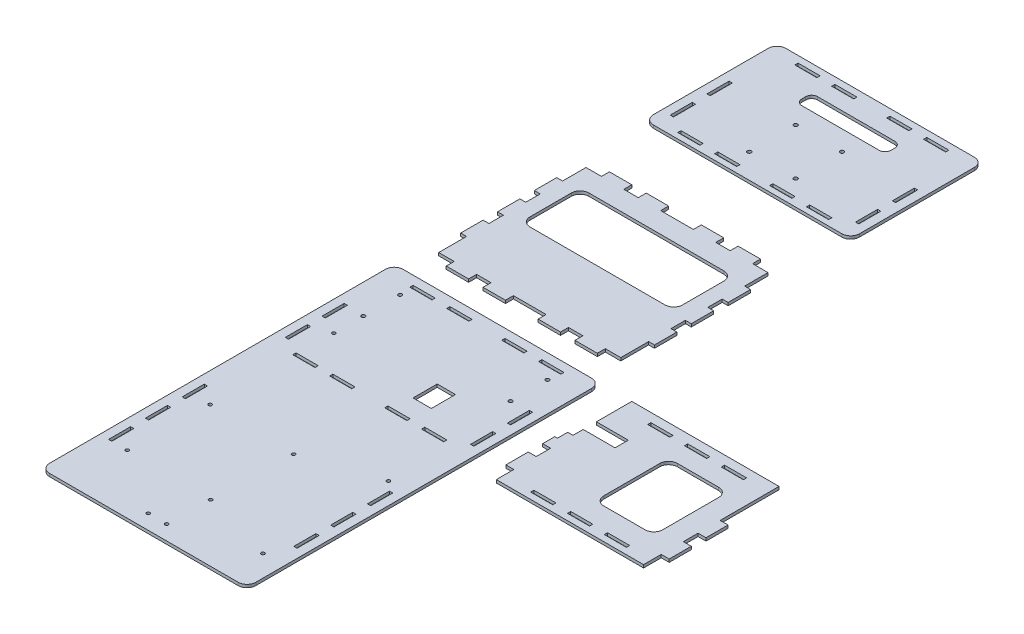
SolidWorks part; units mm, degrees
ref_plane "Front Plane" through (0, 0, 0) normal (0, 0, 1) x (1, 0, 0)
ref_plane "Top Plane" through (0, 0, 0) normal (0, 1, 0) x (1, 0, 0)
ref_plane "Right Plane" through (0, 0, 0) normal (1, 0, 0) x (0, 0, -1)
sketch "Sketch1" plane through (0, 0, 0) normal (0, 1, 0) x (1, 0, 0)
  line L0 (-154.6547, 109.6102) -> (-151.8607, 109.6102)
  line L1 (-154.6547, 192.1602) -> (7.9053, 192.1602)
  line L2 (-162.2747, 184.5402) -> (-162.2747, -105.0198)
  line L3 (-154.6547, -112.6398) -> (7.9053, -112.6398)
  line L4 (15.5253, 184.5402) -> (15.5253, -105.0198)
  line L5 (66.6776, 80.827) -> (66.6776, 83.621)
  line L6 (108.5876, 165.4902) -> (144.1476, 165.4902)
  line L7 (100.9676, 157.8702) -> (100.9676, 109.6102)
  line L8 (108.5876, 101.9902) -> (144.1476, 101.9902)
  line L9 (-154.6547, 109.6102) -> (-154.6547, 90.5602)
  line L10 (-154.6547, 90.5602) -> (-151.8607, 90.5602)
  line L11 (-151.8607, 109.6102) -> (-151.8607, 90.5602)
  line L12 (5.1113, 109.6102) -> (7.9053, 109.6102)
  line L13 (151.7676, 157.8702) -> (151.7676, 109.6102)
  line L14 (-154.6547, -11.0398) -> (-151.8607, -11.0398)
  line L15 (-154.6547, -11.0398) -> (-154.6547, -30.0898)
  line L16 (-154.6547, -30.0898) -> (-151.8607, -30.0898)
  line L17 (5.1113, 109.6102) -> (5.1113, 90.5602)
  line L18 (5.1113, 90.5602) -> (7.9053, 90.5602)
  line L19 (7.9053, 109.6102) -> (7.9053, 90.5602)
  line L20 (5.1113, 141.3602) -> (7.9053, 141.3602)
  line L21 (-154.6547, 141.3602) -> (-151.8607, 141.3602)
  line L22 (-154.6547, 141.3602) -> (-154.6547, 122.3102)
  line L23 (-154.6547, 122.3102) -> (-151.8607, 122.3102)
  line L24 (-151.8607, 141.3602) -> (-151.8607, 122.3102)
  line L25 (5.1113, 141.3602) -> (5.1113, 122.3102)
  line L26 (5.1113, 122.3102) -> (7.9053, 122.3102)
  line L27 (7.9053, 141.3602) -> (7.9053, 122.3102)
  line L28 (-106.6487, 80.827) -> (-106.6487, 83.621)
  line L29 (-106.6487, 80.827) -> (-87.5987, 80.827)
  line L30 (-87.5987, 80.827) -> (-87.5987, 83.621)
  line L31 (-106.6487, 83.621) -> (-87.5987, 83.621)
  line L32 (-138.3987, 80.827) -> (-138.3987, 83.621)
  line L33 (-138.3987, 80.827) -> (-119.3487, 80.827)
  line L34 (-119.3487, 80.827) -> (-119.3487, 83.621)
  line L35 (-138.3987, 83.621) -> (-119.3487, 83.621)
  line L36 (-27.4007, 80.827) -> (-27.4007, 83.621)
  line L37 (-27.4007, 80.827) -> (-8.3507, 80.827)
  line L38 (-8.3507, 80.827) -> (-8.3507, 83.621)
  line L39 (-27.4007, 83.621) -> (-8.3507, 83.621)
  line L40 (-59.1507, 80.827) -> (-59.1507, 83.621)
  line L41 (-59.1507, 80.827) -> (-40.1007, 80.827)
  line L42 (-40.1007, 80.827) -> (-40.1007, 83.621)
  line L43 (-59.1507, 83.621) -> (-40.1007, 83.621)
  line L44 (-106.6487, 181.7462) -> (-106.6487, 184.5402)
  line L45 (-106.6487, 181.7462) -> (-87.5987, 181.7462)
  line L46 (-87.5987, 181.7462) -> (-87.5987, 184.5402)
  line L47 (-106.6487, 184.5402) -> (-87.5987, 184.5402)
  line L48 (-138.3987, 181.7462) -> (-138.3987, 184.5402)
  line L49 (-138.3987, 181.7462) -> (-119.3487, 181.7462)
  line L50 (-119.3487, 181.7462) -> (-119.3487, 184.5402)
  line L51 (-138.3987, 184.5402) -> (-119.3487, 184.5402)
  line L52 (-27.4007, 181.7462) -> (-27.4007, 184.5402)
  line L53 (-27.4007, 181.7462) -> (-8.3507, 181.7462)
  line L54 (-8.3507, 181.7462) -> (-8.3507, 184.5402)
  line L55 (-27.4007, 184.5402) -> (-8.3507, 184.5402)
  line L56 (-59.1507, 181.7462) -> (-59.1507, 184.5402)
  line L57 (-59.1507, 181.7462) -> (-40.1007, 181.7462)
  line L58 (-40.1007, 181.7462) -> (-40.1007, 184.5402)
  line L59 (-59.1507, 184.5402) -> (-40.1007, 184.5402)
  line L60 (35.6896, 109.7372) -> (35.6896, 90.4332)
  line L61 (42.5476, 192.1602) -> (169.5476, 192.1602)
  line L62 (35.6896, 132.5972) -> (35.6896, 122.1832)
  line L63 (42.5476, 75.3202) -> (169.5476, 75.3202)
  line L64 (169.5476, 192.1602) -> (169.5476, 141.3602)
  line L65 (37.9756, 141.4872) -> (42.5476, 141.4872)
  line L66 (42.5476, 161.6802) -> (42.5476, 192.1602)
  line L67 (42.5476, 161.6802) -> (70.0304, 161.6802)
  line L68 (42.5476, 141.4872) -> (42.5476, 150.2502)
  line L69 (35.6896, 122.1832) -> (42.5476, 122.1832)
  line L70 (-106.7757, 213.2329) -> (-87.4717, 213.2329)
  line L71 (35.6896, 109.7372) -> (42.5476, 109.7372)
  line L72 (42.5476, 122.1832) -> (42.5476, 109.7372)
  line L73 (35.6896, 90.4332) -> (42.5476, 90.4332)
  line L74 (42.5476, 150.2502) -> (70.0304, 150.2502)
  line L75 (70.0304, 161.6802) -> (70.0304, 150.2502)
  line L76 (42.5476, 90.4332) -> (42.5476, 75.3202)
  line L77 (-59.2777, 213.2329) -> (-39.9737, 213.2329)
  line L78 (-119.2217, 213.2329) -> (-119.2217, 220.0909)
  line L79 (-119.2217, 220.0909) -> (-106.7757, 220.0909)
  line L80 (-106.7757, 213.2329) -> (-106.7757, 220.0909)
  line L81 (-27.5277, 213.2329) -> (-8.2237, 213.2329)
  line L82 (-87.4717, 213.2329) -> (-87.4717, 220.0909)
  line L83 (-87.4717, 220.0909) -> (-59.2777, 220.0909)
  line L84 (-59.2777, 213.2329) -> (-59.2777, 220.0909)
  line L85 (66.6776, 181.7462) -> (66.6776, 184.5402)
  line L86 (-39.9737, 213.2329) -> (-39.9737, 220.0909)
  line L87 (-39.9737, 220.0909) -> (-27.5277, 220.0909)
  line L88 (-27.5277, 213.2329) -> (-27.5277, 220.0909)
  line L89 (66.6776, 181.7462) -> (85.7276, 181.7462)
  line L90 (-8.2237, 213.2329) -> (-8.2237, 220.0909)
  line L91 (-8.2237, 220.0909) -> (5.1113, 220.0909)
  line L92 (85.7276, 181.7462) -> (85.7276, 184.5402)
  line L93 (-138.5257, 213.2329) -> (-119.2217, 213.2329)
  line L94 (-156.9407, 244.0939) -> (-156.9407, 263.3979)
  line L95 (-151.8607, 347.0909) -> (-138.5257, 347.0909)
  line L96 (10.1913, 244.0939) -> (10.1913, 263.3979)
  line L97 (66.6776, 184.5402) -> (85.7276, 184.5402)
  line L98 (-138.5257, 213.2329) -> (-138.5257, 220.0909)
  line L99 (-138.5257, 220.0909) -> (-151.8607, 220.0909)
  line L100 (130.1776, 181.7462) -> (130.1776, 184.5402)
  line L101 (130.1776, 181.7462) -> (149.2276, 181.7462)
  line L102 (149.2276, 181.7462) -> (149.2276, 184.5402)
  line L103 (130.1776, 184.5402) -> (149.2276, 184.5402)
  line L104 (98.4276, 181.7462) -> (98.4276, 184.5402)
  line L105 (98.4276, 181.7462) -> (117.4776, 181.7462)
  line L106 (117.4776, 181.7462) -> (117.4776, 184.5402)
  line L107 (98.4276, 184.5402) -> (117.4776, 184.5402)
  line L108 (-156.9407, 307.5939) -> (-156.9407, 326.8979)
  line L109 (-151.8607, -11.0398) -> (-151.8607, -30.0898)
  line L110 (5.1113, 347.0909) -> (5.1113, 326.8979)
  line L111 (5.1113, 326.8979) -> (10.1913, 326.8979)
  line L112 (-131.5407, 329.3109) -> (-15.2087, 329.3109)
  line L113 (10.1913, 307.5939) -> (5.1113, 307.5939)
  line L114 (10.1913, 307.5939) -> (10.1913, 326.8979)
  line L115 (10.1913, 295.1479) -> (5.1113, 295.1479)
  line L116 (5.1113, 307.5939) -> (5.1113, 295.1479)
  line L117 (10.1913, 275.8439) -> (5.1113, 275.8439)
  line L118 (-139.1607, 321.6909) -> (-139.1607, 286.1309)
  line L119 (10.1913, 263.3979) -> (5.1113, 263.3979)
  line L120 (5.1113, 275.8439) -> (5.1113, 263.3979)
  line L121 (10.1913, 244.0939) -> (5.1113, 244.0939)
  line L122 (10.1913, 275.8439) -> (10.1913, 295.1479)
  line L123 (-131.5407, 278.5109) -> (-15.2087, 278.5109)
  line L124 (5.1113, 244.0939) -> (5.1113, 220.0909)
  line L125 (-156.9407, 275.8439) -> (-156.9407, 295.1479)
  line L126 (-7.5887, 321.6909) -> (-7.5887, 286.1309)
  line L127 (-156.9407, 326.8979) -> (-151.8607, 326.8979)
  line L128 (-151.8607, 347.0909) -> (-151.8607, 326.8979)
  line L129 (-156.9407, 307.5939) -> (-151.8607, 307.5939)
  line L130 (-154.6547, -42.7898) -> (-151.8607, -42.7898)
  line L131 (-156.9407, 295.1479) -> (-151.8607, 295.1479)
  line L132 (-151.8607, 307.5939) -> (-151.8607, 295.1479)
  line L133 (-156.9407, 275.8439) -> (-151.8607, 275.8439)
  line L134 (-154.6547, -42.7898) -> (-154.6547, -61.8398)
  line L135 (-156.9407, 263.3979) -> (-151.8607, 263.3979)
  line L136 (-151.8607, 275.8439) -> (-151.8607, 263.3979)
  line L137 (-156.9407, 244.0939) -> (-151.8607, 244.0939)
  line L138 (-154.6547, -61.8398) -> (-151.8607, -61.8398)
  line L139 (-151.8607, -42.7898) -> (-151.8607, -61.8398)
  line L140 (-151.8607, 244.0939) -> (-151.8607, 220.0909)
  line L141 (5.1113, -11.0398) -> (7.9053, -11.0398)
  line L142 (5.1113, -11.0398) -> (5.1113, -30.0898)
  line L143 (5.1113, -30.0898) -> (7.9053, -30.0898)
  line L144 (7.9053, -11.0398) -> (7.9053, -30.0898)
  line L145 (7.9053, -42.7898) -> (5.1113, -42.7898)
  line L146 (7.9053, -42.7898) -> (7.9053, -61.8398)
  line L147 (7.9053, -61.8398) -> (5.1113, -61.8398)
  line L148 (5.1113, -42.7898) -> (5.1113, -61.8398)
  line L149 (5.1113, 1.6602) -> (7.9053, 1.6602)
  line L150 (5.1113, 1.6602) -> (5.1113, 20.7102)
  line L151 (5.1113, 20.7102) -> (7.9053, 20.7102)
  line L152 (7.9053, 1.6602) -> (7.9053, 20.7102)
  line L153 (-154.6547, 1.6602) -> (-151.8607, 1.6602)
  line L154 (-154.6547, 1.6602) -> (-154.6547, 20.7102)
  line L155 (-154.6547, 20.7102) -> (-151.8607, 20.7102)
  line L156 (-151.8607, 1.6602) -> (-151.8607, 20.7102)
  line L157 (-54.3315, 121.2429) -> (-38.5835, 121.2429)
  line L158 (-54.3315, 121.2429) -> (-54.3315, 100.4149)
  line L159 (-54.3315, 100.4149) -> (-38.5835, 100.4149)
  line L160 (-38.5835, 121.2429) -> (-38.5835, 100.4149)
  line L161 (66.6776, 80.827) -> (85.7276, 80.827)
  line L162 (85.7276, 80.827) -> (85.7276, 83.621)
  line L163 (66.6776, 83.621) -> (85.7276, 83.621)
  line L164 (130.1776, 80.827) -> (130.1776, 83.621)
  line L165 (130.1776, 80.827) -> (149.2276, 80.827)
  line L166 (149.2276, 80.827) -> (149.2276, 83.621)
  line L167 (130.1776, 83.621) -> (149.2276, 83.621)
  line L168 (98.4276, 80.827) -> (98.4276, 83.621)
  line L169 (98.4276, 80.827) -> (117.4776, 80.827)
  line L170 (117.4776, 80.827) -> (117.4776, 83.621)
  line L171 (98.4276, 83.621) -> (117.4776, 83.621)
  line L172 (169.5476, 122.3102) -> (169.5476, 109.6102)
  line L173 (169.5476, 90.5602) -> (176.4056, 90.5602)
  line L174 (-119.2217, 347.0909) -> (-106.7757, 347.0909)
  line L175 (35.6896, 132.5972) -> (37.9756, 132.5972)
  line L176 (37.9756, 141.4872) -> (37.9756, 132.5972)
  line L177 (169.5476, 109.6102) -> (176.4056, 109.6102)
  line L178 (176.4056, 90.5602) -> (176.4056, 109.6102)
  line L179 (169.5476, 122.3102) -> (176.4056, 122.3102)
  line L180 (169.5476, 90.5602) -> (169.5476, 75.3202)
  line L181 (169.5476, 141.3602) -> (176.4056, 141.3602)
  line L182 (176.4056, 122.3102) -> (176.4056, 141.3602)
  line L183 (-87.4717, 347.0909) -> (-59.2777, 347.0909)
  line L184 (-138.5257, 347.0909) -> (-138.5257, 353.9489)
  line L185 (-138.5257, 353.9489) -> (-119.2217, 353.9489)
  line L186 (-119.2217, 347.0909) -> (-119.2217, 353.9489)
  line L187 (-39.9737, 347.0909) -> (-27.5277, 347.0909)
  line L188 (-106.7757, 347.0909) -> (-106.7757, 353.9489)
  line L189 (-106.7757, 353.9489) -> (-87.4717, 353.9489)
  line L190 (-87.4717, 347.0909) -> (-87.4717, 353.9489)
  line L191 (-8.2237, 347.0909) -> (5.1113, 347.0909)
  line L192 (-59.2777, 347.0909) -> (-59.2777, 353.9489)
  line L193 (-59.2777, 353.9489) -> (-39.9737, 353.9489)
  line L194 (-39.9737, 347.0909) -> (-39.9737, 353.9489)
  line L195 (-154.6547, 441.5523) -> (-151.8607, 441.5523)
  line L196 (-27.5277, 347.0909) -> (-27.5277, 353.9489)
  line L197 (-27.5277, 353.9489) -> (-8.2237, 353.9489)
  line L198 (-8.2237, 347.0909) -> (-8.2237, 353.9489)
  line L199 (-154.6547, 407.9203) -> (7.9053, 407.9203)
  line L200 (-162.2747, 415.5403) -> (-162.2747, 514.6003)
  line L201 (-154.6547, 522.2203) -> (7.9053, 522.2203)
  line L202 (15.5253, 415.5403) -> (15.5253, 514.6003)
  line L203 (-154.6547, 441.5523) -> (-154.6547, 422.5023)
  line L204 (-154.6547, 422.5023) -> (-151.8607, 422.5023)
  line L205 (-151.8607, 441.5523) -> (-151.8607, 422.5023)
  line L206 (5.1113, 441.5523) -> (7.9053, 441.5523)
  line L207 (5.1113, 441.5523) -> (5.1113, 422.5023)
  line L208 (5.1113, 422.5023) -> (7.9053, 422.5023)
  line L209 (7.9053, 441.5523) -> (7.9053, 422.5023)
  line L210 (5.1113, 473.3023) -> (7.9053, 473.3023)
  line L211 (-154.6547, 473.3023) -> (-151.8607, 473.3023)
  line L212 (-154.6547, 473.3023) -> (-154.6547, 454.2523)
  line L213 (-154.6547, 454.2523) -> (-151.8607, 454.2523)
  line L214 (-151.8607, 473.3023) -> (-151.8607, 454.2523)
  line L215 (5.1113, 473.3023) -> (5.1113, 454.2523)
  line L216 (5.1113, 454.2523) -> (7.9053, 454.2523)
  line L217 (7.9053, 473.3023) -> (7.9053, 454.2523)
  line L218 (-106.6487, 412.769) -> (-106.6487, 415.563)
  line L219 (-106.6487, 412.769) -> (-87.5987, 412.769)
  line L220 (-87.5987, 412.769) -> (-87.5987, 415.563)
  line L221 (-106.6487, 415.563) -> (-87.5987, 415.563)
  line L222 (-138.3987, 412.769) -> (-138.3987, 415.563)
  line L223 (-138.3987, 412.769) -> (-119.3487, 412.769)
  line L224 (-119.3487, 412.769) -> (-119.3487, 415.563)
  line L225 (-138.3987, 415.563) -> (-119.3487, 415.563)
  line L226 (-27.4007, 412.769) -> (-27.4007, 415.563)
  line L227 (-27.4007, 412.769) -> (-8.3507, 412.769)
  line L228 (-8.3507, 412.769) -> (-8.3507, 415.563)
  line L229 (-27.4007, 415.563) -> (-8.3507, 415.563)
  line L230 (-59.1507, 412.769) -> (-59.1507, 415.563)
  line L231 (-59.1507, 412.769) -> (-40.1007, 412.769)
  line L232 (-40.1007, 412.769) -> (-40.1007, 415.563)
  line L233 (-59.1507, 415.563) -> (-40.1007, 415.563)
  line L234 (-106.6487, 513.6883) -> (-106.6487, 516.4823)
  line L235 (-106.6487, 513.6883) -> (-87.5987, 513.6883)
  line L236 (-87.5987, 513.6883) -> (-87.5987, 516.4823)
  line L237 (-106.6487, 516.4823) -> (-87.5987, 516.4823)
  line L238 (-138.3987, 513.6883) -> (-138.3987, 516.4823)
  line L239 (-138.3987, 513.6883) -> (-119.3487, 513.6883)
  line L240 (-119.3487, 513.6883) -> (-119.3487, 516.4823)
  line L241 (-138.3987, 516.4823) -> (-119.3487, 516.4823)
  line L242 (-27.4007, 513.6883) -> (-27.4007, 516.4823)
  line L243 (-27.4007, 513.6883) -> (-8.3507, 513.6883)
  line L244 (-8.3507, 513.6883) -> (-8.3507, 516.4823)
  line L245 (-27.4007, 516.4823) -> (-8.3507, 516.4823)
  line L246 (-59.1507, 513.6883) -> (-59.1507, 516.4823)
  line L247 (-59.1507, 513.6883) -> (-40.1007, 513.6883)
  line L248 (-40.1007, 513.6883) -> (-40.1007, 516.4823)
  line L249 (-59.1507, 516.4823) -> (-40.1007, 516.4823)
  line L251 (-104.9571, 499.8379) -> (-38.2492, 499.8379)
  line L252 (-110.0371, 494.7579) -> (-110.0371, 491.4023)
  line L253 (-104.9571, 486.3223) -> (-38.2492, 486.3223)
  line L254 (-33.1692, 494.7579) -> (-33.1692, 491.4023)
  arc A0 (15.5253, -105.0198) -> (7.9053, -112.6398) centre (7.9053, -105.0198) cw
  arc A1 (-154.6547, -112.6398) -> (-162.2747, -105.0198) centre (-154.6547, -105.0198) cw
  arc A2 (15.5253, 184.5402) -> (7.9053, 192.1602) centre (7.9053, 184.5402) ccw
  arc A3 (-154.6547, 192.1602) -> (-162.2747, 184.5402) centre (-154.6547, 184.5402) ccw
  circle A4 centre (-136.8747, 171.8402) radius 1.5875
  circle A5 centre (-136.8747, 140.0902) radius 1.5875
  circle A6 centre (-9.8747, 171.8402) radius 1.5875
  circle A7 centre (-9.8747, 140.0902) radius 1.5875
  circle A8 centre (-136.8747, 8.0102) radius 1.4478
  circle A9 centre (-63.8497, 6.9149) radius 1.4478
  circle A10 centre (-65.5963, -62.9132) radius 1.4478
  circle A11 centre (-138.6213, -61.8398) radius 1.4478
  circle A12 centre (-82.2647, -99.9398) radius 1.4478
  circle A13 centre (-66.3899, -100.0159) radius 1.4478
  arc A14 (144.1476, 165.4902) -> (151.7676, 157.8702) centre (144.1476, 157.8702) cw
  arc A15 (100.9676, 109.6102) -> (108.5876, 101.9902) centre (108.5876, 109.6102) ccw
  arc A16 (144.1476, 101.9902) -> (151.7676, 109.6102) centre (144.1476, 109.6102) ccw
  arc A17 (108.5876, 165.4902) -> (100.9676, 157.8702) centre (108.5876, 157.8702) ccw
  circle A18 centre (-93.1805, 469.1947) radius 1.65
  circle A19 centre (-53.1805, 469.1947) radius 1.65
  circle A20 centre (-53.1805, 429.1947) radius 1.65
  circle A21 centre (-93.1805, 429.1947) radius 1.65
  arc A22 (-15.2087, 329.3109) -> (-7.5887, 321.6909) centre (-15.2087, 321.6909) cw
  arc A23 (-139.1607, 286.1309) -> (-131.5407, 278.5109) centre (-131.5407, 286.1309) ccw
  arc A24 (-15.2087, 278.5109) -> (-7.5887, 286.1309) centre (-15.2087, 286.1309) ccw
  arc A25 (-131.5407, 329.3109) -> (-139.1607, 321.6909) centre (-131.5407, 321.6909) ccw
  circle A26 centre (-2.9506, -80.4342) radius 1.4478
  circle A27 centre (-2.9506, 27.7504) radius 1.4478
  circle A28 centre (-136.8747, 114.6902) radius 1.4478
  arc A29 (-162.2747, 415.5403) -> (-154.6547, 407.9203) centre (-154.6547, 415.5403) ccw
  arc A30 (15.5253, 514.6003) -> (7.9053, 522.2203) centre (7.9053, 514.6003) ccw
  arc A31 (7.9053, 407.9203) -> (15.5253, 415.5403) centre (7.9053, 415.5403) ccw
  arc A32 (-154.6547, 522.2203) -> (-162.2747, 514.6003) centre (-154.6547, 514.6003) ccw
  arc A33 (-38.2492, 499.8379) -> (-33.1692, 494.7579) centre (-38.2492, 494.7579) cw
  arc A34 (-110.0371, 491.4023) -> (-104.9571, 486.3223) centre (-104.9571, 491.4023) ccw
  arc A35 (-38.2492, 486.3223) -> (-33.1692, 491.4023) centre (-38.2492, 491.4023) ccw
  arc A36 (-104.9571, 499.8379) -> (-110.0371, 494.7579) centre (-104.9571, 494.7579) ccw
  dimension "D3" = 7.62
  dimension "D8" = 69.85
  dimension "D21" = 17.78
  dimension "D22" = 17.78
  dimension "D23" = 6.858
  dimension "D93" = 7.62
  dimension "D95" = 2.8956
  dimension "D96" = 2.8956
  dimension "D97" = 2.8956
  dimension "D98" = 2.8956
  dimension "D99" = 2.8956
  dimension "D100" = 2.8956
  dimension "D101" = 2.8956
  dimension "D102" = 2.8956
  dimension "D103" = 2.8956
  dimension "D27" = 7.62
  dimension "D110" = 3.3
  dimension "D111" = 3.3
  dimension "D112" = 3.3
  dimension "D113" = 3.3
  dimension "D117" = 7.62
  dimension "D118" = 5.08
  dimension "D1" = 304.8
  dimension "D2" = 177.8
  dimension "D5" = 25.4
  dimension "D6" = 25.4
  dimension "D9" = 73.025
  dimension "D10" = 25.4
  dimension "D11" = 69.85
  dimension "D12" = 73.025
  dimension "D13" = 50.8
  dimension "D14" = 15.875
  dimension "D15" = 80.01
  dimension "D16" = 12.7
  dimension "D17" = 25.4
  dimension "D18" = 25.4
  dimension "D19" = 20.32
  dimension "D20" = 4.572
  dimension "D24" = 2.794
  dimension "D25" = 127
  dimension "D26" = 13.462
  dimension "D28" = 7.62
  dimension "D29" = 7.62
  dimension "D30" = 50.8
  dimension "D31" = 50.8
  dimension "D32" = 19.05
  dimension "D33" = 19.05
  dimension "D34" = 12.7
  dimension "D35" = 2.794
  dimension "D36" = 50.8
  dimension "D37" = 13.335
  dimension "D38" = 19.304
  dimension "D39" = 12.446
  dimension "D40" = 19.304
  dimension "D41" = 13.335
  dimension "D42" = 19.304
  dimension "D43" = 12.446
  dimension "D44" = 19.304
  dimension "D45" = 31.75
  dimension "D46" = 26.67
  dimension "D47" = 63.5
  dimension "D48" = 2.794
  dimension "D49" = 7.62
  dimension "D50" = 2.794
  dimension "D51" = 50.8
  dimension "D52" = 13.462
  dimension "D53" = 19.05
  dimension "D54" = 12.7
  dimension "D55" = 19.05
  dimension "D56" = 12.7
  dimension "D57" = 19.05
  dimension "D58" = 12.7
  dimension "D59" = 19.05
  dimension "D60" = 19.05
  dimension "D61" = 12.7
  dimension "D62" = 19.05
  dimension "D63" = 12.7
  dimension "D64" = 12.7
  dimension "D65" = 19.05
  dimension "D66" = 20.828
  dimension "D67" = 6.858
  dimension "D68" = 50.673
  dimension "D69" = 19.304
  dimension "D70" = 0
  dimension "D71" = 12.446
  dimension "D72" = 19.304
  dimension "D73" = 10.16
  dimension "D74" = 10.16
  dimension "D75" = 27.4828
  dimension "D76" = 127
  dimension "D77" = 15.748
  dimension "D78" = 8.89
  dimension "D79" = 20.32
  dimension "D80" = 19.05
  dimension "D81" = 19.05
  dimension "D82" = 19.05
  dimension "D83" = 12.7
  dimension "D84" = 12.7
  dimension "D85" = 5.08
  dimension "D86" = 20.193
  dimension "D87" = 19.304
  dimension "D88" = 19.304
  dimension "D89" = 19.304
  dimension "D90" = 12.446
  dimension "D91" = 12.446
  dimension "D92" = 5.08
  dimension "D94" = 116.84
  dimension "D104" = 7.62
  dimension "D105" = 6.858
  dimension "D106" = 6.858
  dimension "D107" = 114.3
  dimension "D108" = 108.5393
  dimension "D109" = 2.794
  dimension "D114" = 40
  dimension "D115" = 2.794
  dimension "D116" = 40
extrude "Boss-Extrude1" add sketch "Sketch1" along normal blind 2.54
